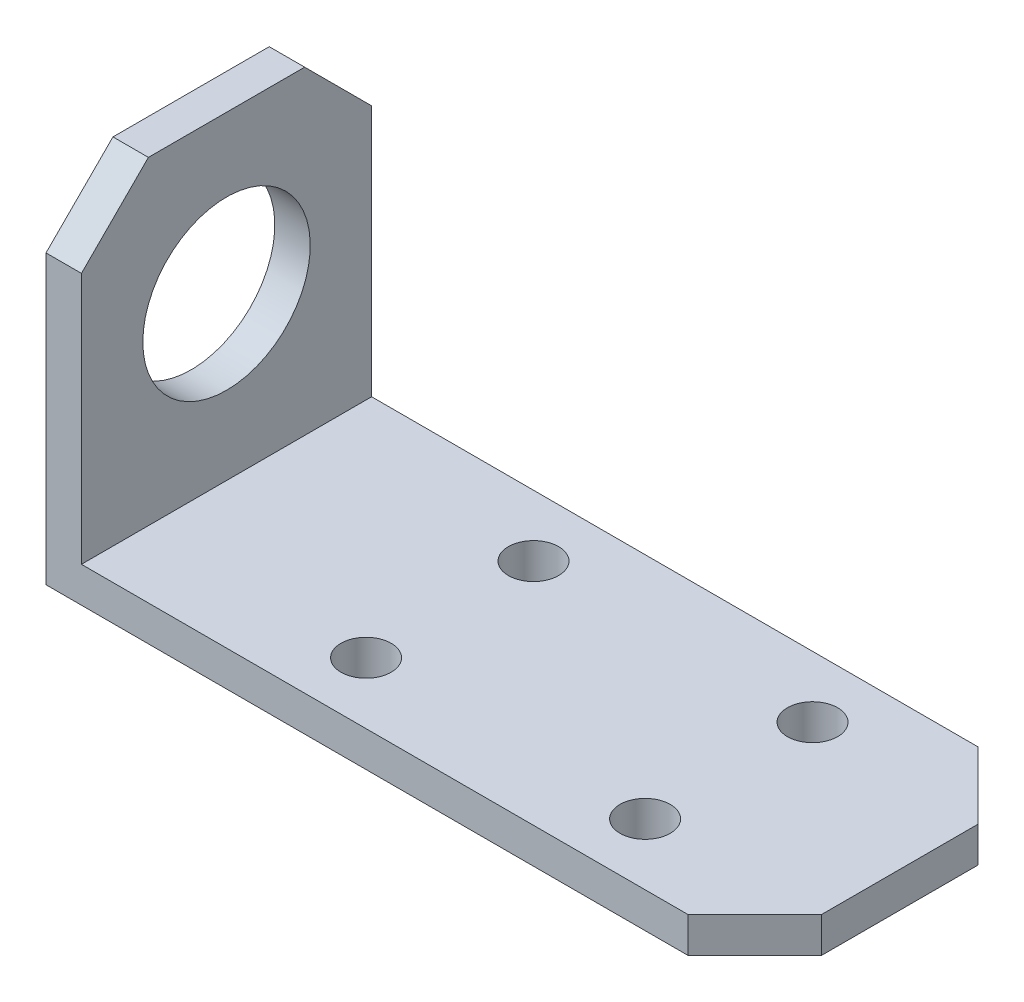
SolidWorks part; units mm, degrees
material "6061-T6 (SS)"
ref_plane "Front Plane" through (0, 0, 0) normal (0, 0, 1) x (1, 0, 0)
ref_plane "Top Plane" through (0, 0, 0) normal (0, 1, 0) x (1, 0, 0)
ref_plane "Right Plane" through (0, 0, 0) normal (1, 0, 0) x (0, 0, -1)
sketch "Sketch1" plane through (0, 0, 0) normal (0, 0, 1) x (1, 0, 0)
  line L0 (0, 0) -> (0, 31.75)
  line L1 (0, 31.75) -> (3.175, 31.75)
  line L2 (3.175, 31.75) -> (3.175, 3.175)
  line L3 (3.175, 3.175) -> (63.5, 3.175)
  line L4 (63.5, 3.175) -> (63.5, 0)
  line L5 (63.5, 0) -> (0, 0)
  dimension "D1" = 3.175
  dimension "D2" = 31.75
  dimension "D3" = 63.5
extrude "Boss-Extrude1" add sketch "Sketch1" along normal blind 26
sketch "Sketch4" plane through (0, 3.175, 0) normal (0, 1, 0) x (1, 0, 0)
  line L0 (3.175, -26) -> (3.175, 0) construction
  point P0 (23.175, -20.5)
  point P2 (23.175, -5.5)
  point P4 (48.175, -5.5)
  point P6 (48.175, -20.5)
  point P16 (3.175, -13)
  dimension "D1" = 15
  dimension "D2" = 25
  dimension "D3" = 20
  dimension "D4" = 7.5
hole_wizard "M4 Clearance Hole1" positions "Sketch4" profile "Sketch3" hole size "M4" standard "ANSI Metric" end condition through all
sketch "Sketch3" plane through (23.175, 3.175, 20.5) normal (1, 0, 0) x (0, 0, 1)
  line L0 (0, 0) -> (0, 3.175)
  line L1 (0, 3.175) -> (2.25, 3.175)
  line L2 (2.25, 3.175) -> (2.25, 0)
  line L5 (2.25, 0) -> (0, 0)
  line L11 (0, -6.35) -> (0, 107.95) construction
  dimension "Thru Hole Dia." = 4.5
  dimension "Thru Hole Depth" = 3.175
sketch "Sketch5" plane through (0, 0, 0) normal (-1, 0, 0) x (0, 0, 1)
  line L0 (0, 31.75) -> (0, 0) construction
  line L1 (26, 0) -> (0, 0) construction
  circle A0 centre (13, 17.675) radius 7.5
  dimension "D1" = 15
  dimension "D2" = 13
  dimension "D3" = 17.675
extrude "Cut-Extrude1" cut sketch "Sketch5" against normal through all
chamfer "Chamfer1" distance 6 angle 45 4 edges at (63.5, 1.5875, 26) (63.5, 1.5875, 0) (1.5875, 31.75, 0) (1.5875, 31.75, 26)
